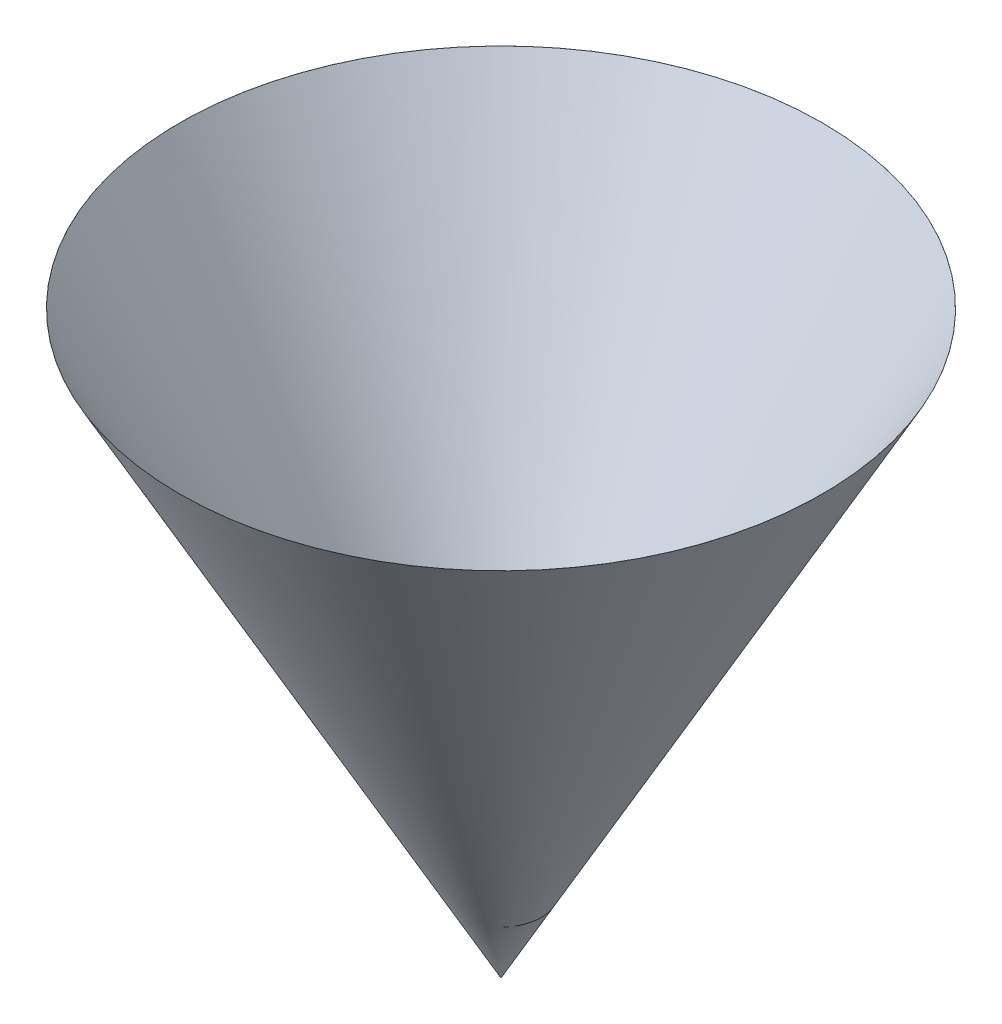
SolidWorks part; units mm, degrees
ref_plane "前视基准面" through (0, 0, 0) normal (0, 0, 1) x (1, 0, 0)
ref_plane "上视基准面" through (0, 0, 0) normal (0, 1, 0) x (1, 0, 0)
ref_plane "右视基准面" through (0, 0, 0) normal (1, 0, 0) x (0, 0, -1)
sketch "草图2" plane through (0, 0, 0) normal (1, 0, 0) x (0, 0, -1)
  line L0 (0, 0) -> (0, 27.0153) construction
  line L1 (0, 0) -> (83.1464, 150)
  line L2 (83.1464, 150) -> (83.1364, 150)
  line L3 (83.1364, 150) -> (0, 0.018)
  line L4 (0, 0.018) -> (0, 0)
  dimension "D1" = 29
  dimension "D2" = 0.01
  dimension "D3" = 150
revolve "旋转1" add sketch "草图2" angle 360 about L0
